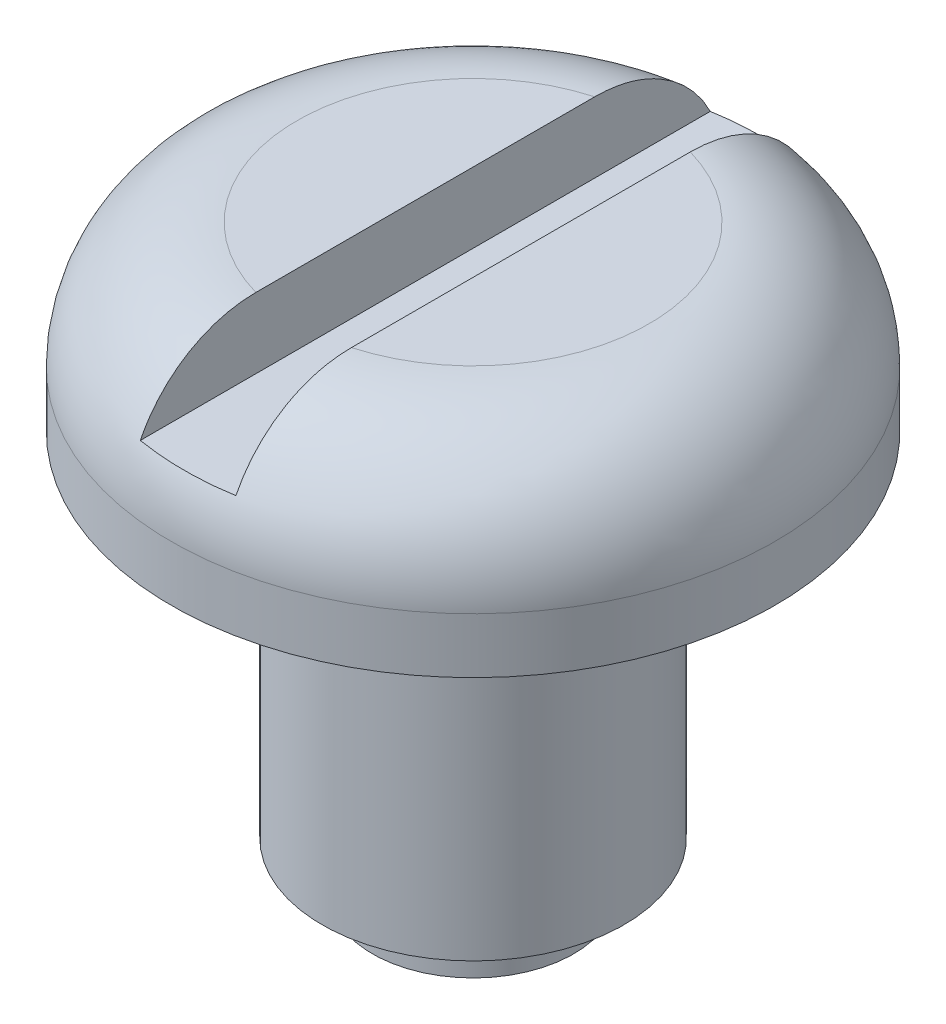
SolidWorks part; units mm, degrees
ref_plane "Front Plane" through (0, 0, 0) normal (0, 0, 1) x (1, 0, 0)
ref_plane "Top Plane" through (0, 0, 0) normal (0, 1, 0) x (1, 0, 0)
ref_plane "Right Plane" through (0, 0, 0) normal (1, 0, 0) x (0, 0, -1)
sketch "Sketch1" plane through (0, 0, 0) normal (0, 0, 1) x (1, 0, 0)
  line L0 (0, 0) -> (0, 11.8942) construction
  line L1 (0, 0) -> (2, 0)
  line L2 (2, 0) -> (2, 1)
  line L3 (2, 1) -> (3, 1)
  line L4 (3, 1) -> (3, 8)
  line L5 (3, 8) -> (6, 8)
  line L6 (6, 8) -> (6, 9.1)
  line L7 (3.5, 11.6) -> (0, 11.6)
  line L8 (0, 0) -> (0, 11.6)
  arc A0 (6, 9.1) -> (3.5, 11.6) centre (3.5, 9.1) ccw
  point P12 (6, 11.6)
  dimension "D7" = 2.5
  dimension "D1" = 4
  dimension "D2" = 6
  dimension "D3" = 1
  dimension "D4" = 7
  dimension "D5" = 3.6
  dimension "D6" = 12
revolve "Revolve1" add sketch "Sketch1" angle 360 about L0
cosmetic thread "Cosmetic Thread2" parameters "D2"=4.891
cosmetic thread "Cosmetic Thread3" parameters "D2"=4.891
sketch "Sketch2" plane through (0, 0, 0) normal (0, 0, 1) x (1, 0, 0)
  line L0 (3.5, 11.6) -> (-3.5, 11.6) construction
  line L1 (-0.95, 11.6) -> (0.95, 11.6)
  line L2 (-0.95, 11.6) -> (-0.95, 10.2)
  line L3 (-0.95, 10.2) -> (0.95, 10.2)
  line L4 (0.95, 11.6) -> (0.95, 10.2)
  line L5 (0, 0) -> (0, 12.8884) construction
  dimension "D1" = 1.9
  dimension "D2" = 1.4
extrude "Cut-Extrude1" cut sketch "Sketch2" against normal through all both and the other way through all
